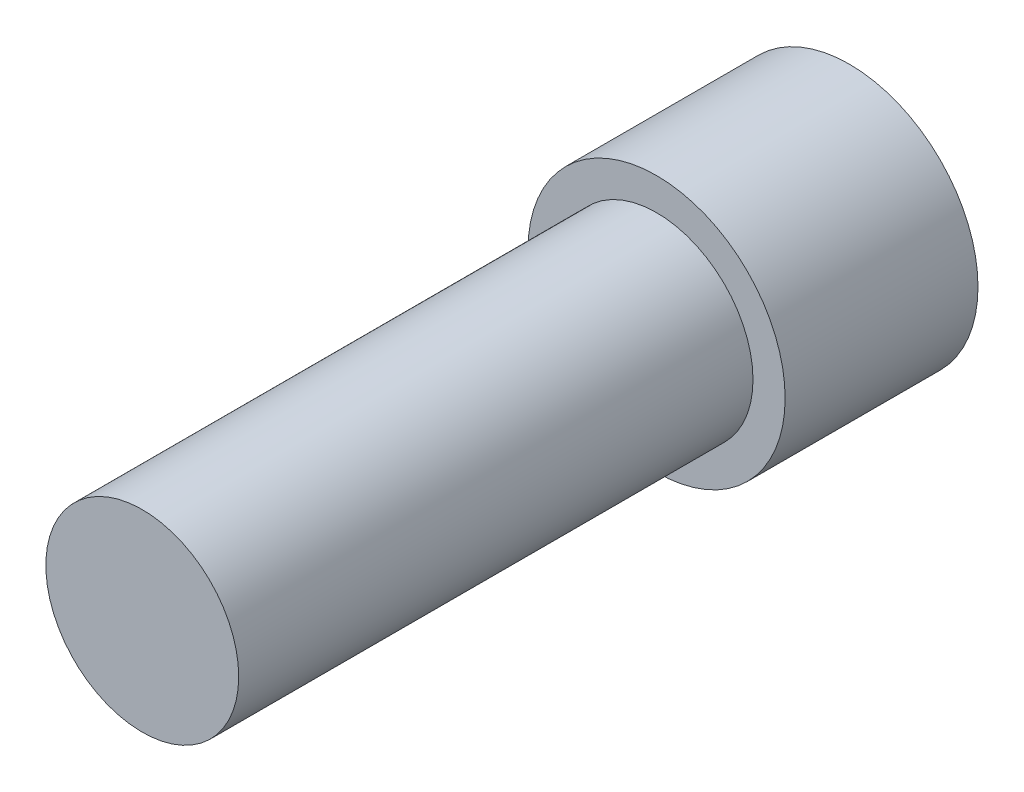
SolidWorks part; units mm, degrees
ref_plane "前视基准面" through (0, 0, 0) normal (0, 0, 1) x (1, 0, 0)
ref_plane "上视基准面" through (0, 0, 0) normal (0, 1, 0) x (1, 0, 0)
ref_plane "右视基准面" through (0, 0, 0) normal (1, 0, 0) x (0, 0, -1)
sketch "草图1" plane through (0, 0, 0) normal (0, 0, 1) x (1, 0, 0)
  circle A0 centre (0, 0) radius 2
  dimension "D1" = 4
extrude "凸台-拉伸1" add sketch "草图1" along normal blind 3
sketch "草图2" plane through (0, 0, 3) normal (0, 0, 1) x (1, 0, 0)
  circle A0 centre (0, 0) radius 1.5
  dimension "D1" = 3
extrude "凸台-拉伸2" add sketch "草图2" along normal blind 8
sketch "草图3" plane through (0, 0, 0) normal (0, 0, -1) x (-1, 0, 0)
  line L1 (1.5139, -0.8416) -> (1.4857, 0.8903)
  line L2 (1.4857, 0.8903) -> (-0.0281, 1.7318)
  line L3 (-0.0281, 1.7318) -> (-1.5139, 0.8416)
  line L4 (-1.5139, 0.8416) -> (-1.4857, -0.8903)
  line L5 (-1.4857, -0.8903) -> (0.0281, -1.7318)
  line L6 (0.0281, -1.7318) -> (1.5139, -0.8416)
  circle A0 centre (0, 0) radius 1.5 construction
  dimension "D1" = 3
extrude "切除-拉伸1" cut sketch "草图3" against normal blind 2
